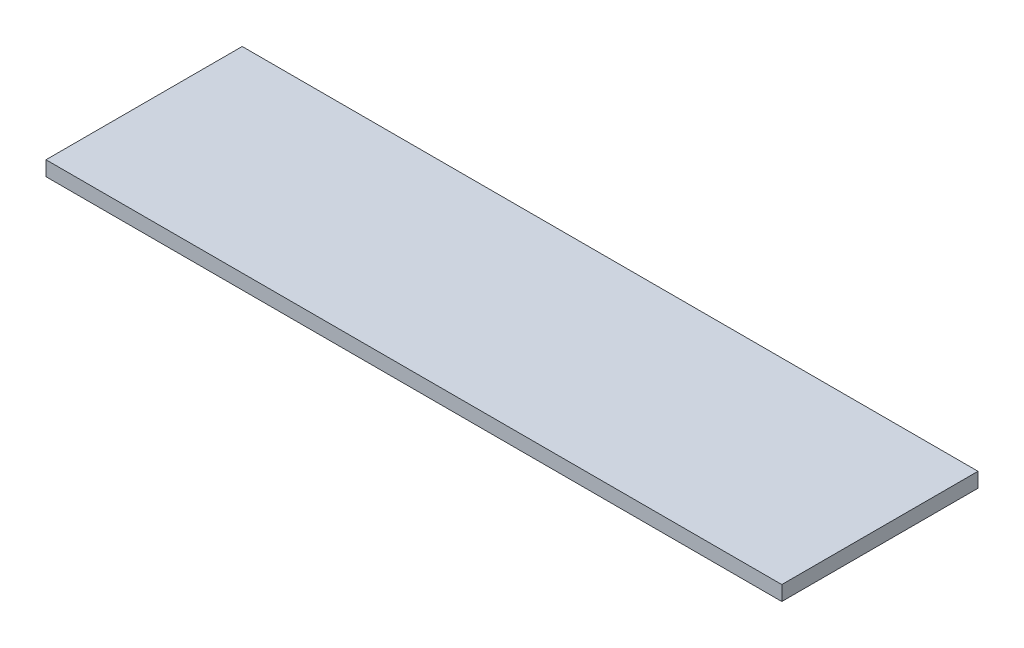
SolidWorks part; units mm, degrees
other "Marquage1"
sketch "Esquisse2"
other "Marquage3"
sketch "Esquisse4"
material "Caoutchouc"
ref_plane "Plan de face" through (0, 0, 0) normal (0, 0, 1) x (1, 0, 0)
ref_plane "Plan de dessus" through (0, 0, 0) normal (0, 1, 0) x (1, 0, 0)
ref_plane "Plan de droite" through (0, 0, 0) normal (1, 0, 0) x (0, 0, -1)
sketch "Esquisse1" plane through (0, 0, 0) normal (0, 0, 1) x (1, 0, 0)
  line L1 (150, -3) -> (-150, -3)
  line L2 (150, -3) -> (150, 3)
  line L3 (150, 3) -> (-150, 3)
  line L4 (-150, -3) -> (-150, 3)
  line L5 (150, -3) -> (-150, 3) construction
  line L6 (150, 3) -> (-150, -3) construction
  point P0 (0, 0)
  dimension "D1" = 300
  dimension "D2" = 6
extrude "Boss.-Extru.1" add sketch "Esquisse1" along normal blind 80
